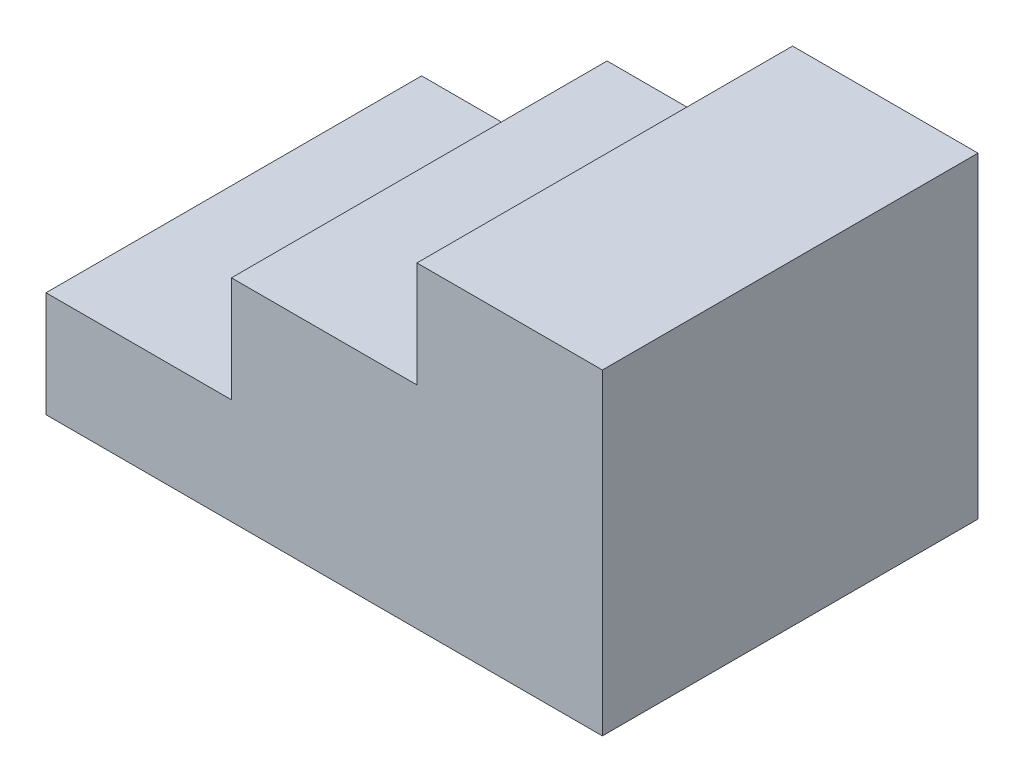
SolidWorks part; units mm, degrees
ref_plane "Front Plane" through (0, 0, 0) normal (0, 0, 1) x (1, 0, 0)
ref_plane "Top Plane" through (0, 0, 0) normal (0, 1, 0) x (1, 0, 0)
ref_plane "Right Plane" through (0, 0, 0) normal (1, 0, 0) x (0, 0, -1)
sketch "Sketch1" plane through (0, 0, 0) normal (0, 0, 1) x (1, 0, 0)
  line L0 (0, 0) -> (902.97, 0)
  line L1 (902.97, 0) -> (902.97, 514.35)
  line L2 (902.97, 514.35) -> (601.98, 514.35)
  line L3 (601.98, 514.35) -> (601.98, 342.9)
  line L4 (601.98, 342.9) -> (300.99, 342.9)
  line L5 (300.99, 342.9) -> (300.99, 171.45)
  line L6 (300.99, 171.45) -> (0, 171.45)
  line L7 (0, 171.45) -> (0, 0)
  dimension "D1" = 171.45
  dimension "D2" = 171.45
  dimension "D3" = 171.45
  dimension "D4" = 300.99
  dimension "D5" = 300.99
  dimension "D6" = 300.99
extrude "Boss-Extrude1" add sketch "Sketch1" along normal blind 609.6
